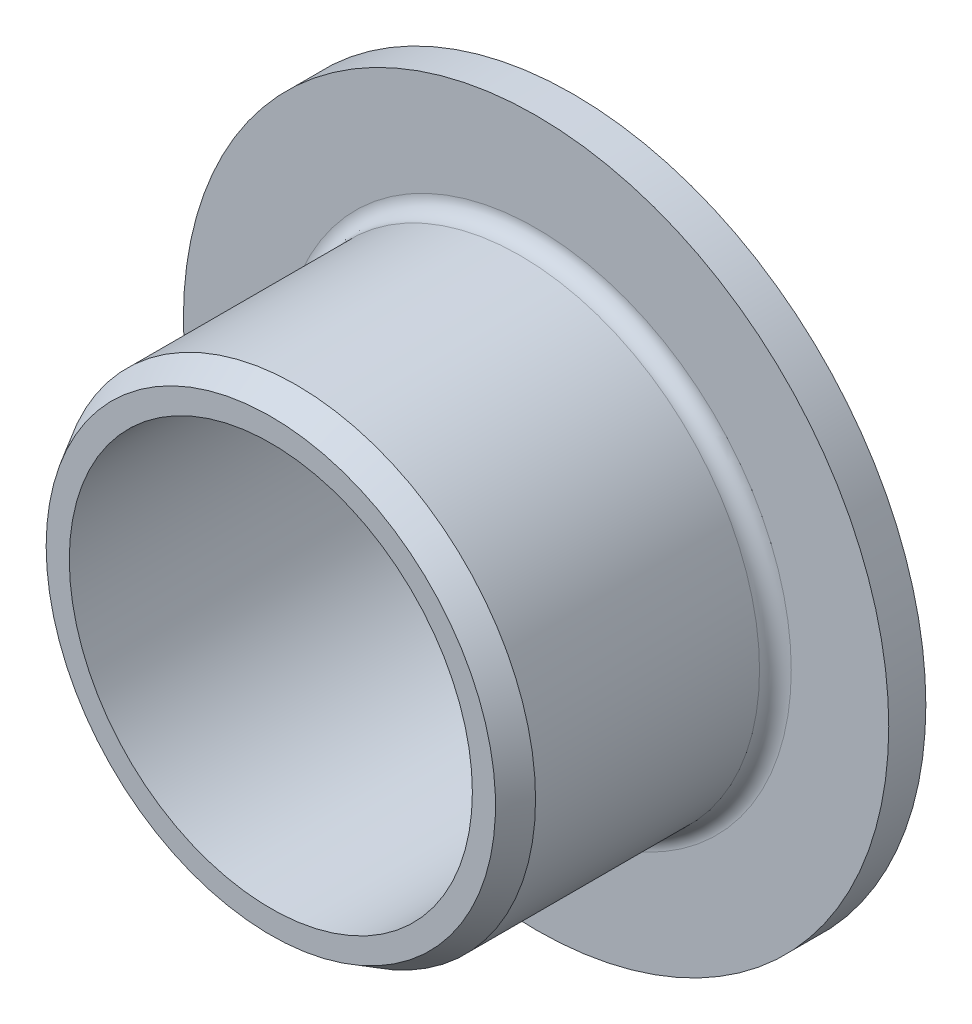
SolidWorks part; units mm, degrees
ref_plane "Front Plane" through (0, 0, 0) normal (0, 0, 1) x (1, 0, 0)
ref_plane "Top Plane" through (0, 0, 0) normal (0, 1, 0) x (1, 0, 0)
ref_plane "Right Plane" through (0, 0, 0) normal (1, 0, 0) x (0, 0, -1)
ref_plane "Plane1" through (0, 0, 0) normal (0, -1, 0) x (1, 0, 0)
sketch "Sketch1" plane through (0, 0, 0) normal (0, -1, 0) x (1, 0, 0)
  line L0 (7.5406, 1.6684) -> (7.5406, 8.725)
  line L1 (7.5406, 8.725) -> (7.0787, 9.525)
  line L2 (7.0787, 9.525) -> (6.35, 9.525)
  line L3 (6.35, 9.525) -> (6.35, 0)
  line L4 (6.35, 0) -> (11.1125, 0)
  line L5 (11.1125, 0) -> (11.1125, 1.1684)
  line L6 (11.1125, 1.1684) -> (8.0406, 1.1684)
  line L7 (0, 9.525) -> (0, 0) construction
  arc A0 (8.0406, 1.1684) -> (7.5406, 1.6684) centre (8.0406, 1.6684) cw
revolve "Revolve1" add sketch "Sketch1" angle 360 about L7
